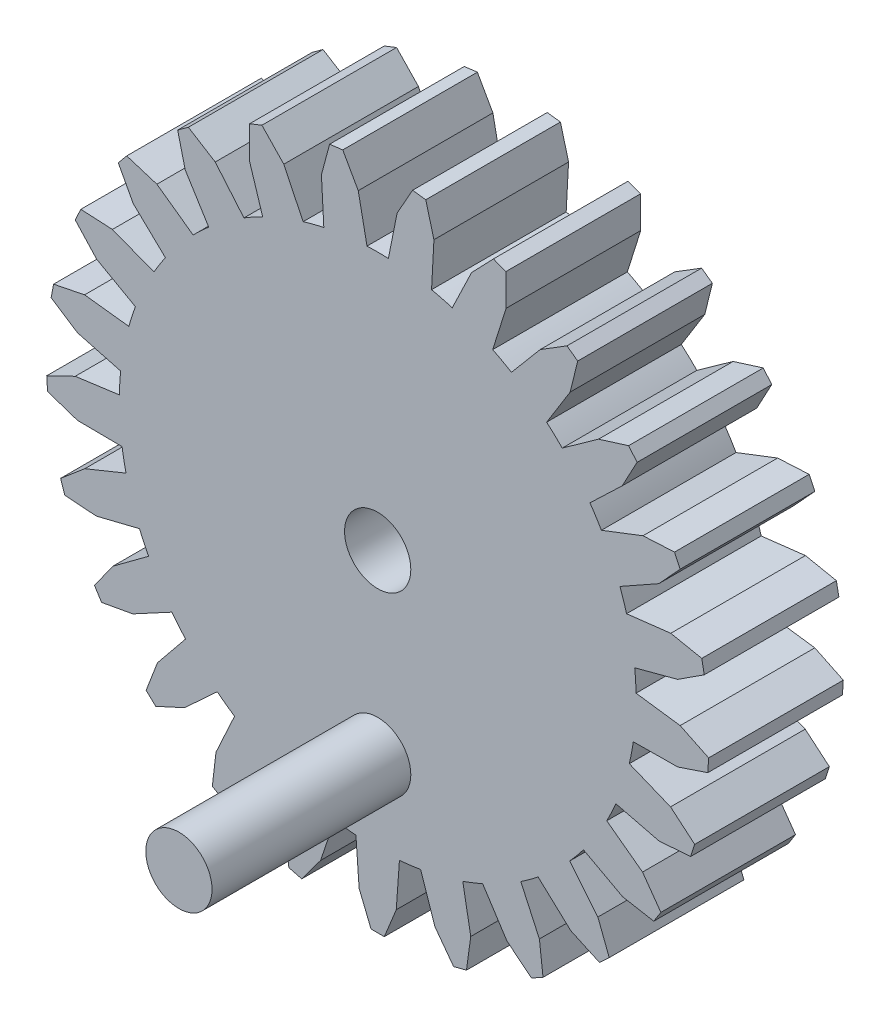
SolidWorks part; units mm, degrees
ref_plane "Front Plane" through (0, 0, 0) normal (0, 0, 1) x (1, 0, 0)
ref_plane "Top Plane" through (0, 0, 0) normal (0, 1, 0) x (1, 0, 0)
ref_plane "Right Plane" through (0, 0, 0) normal (1, 0, 0) x (0, 0, -1)
sketch "Sketch1" plane through (0, 0, 0) normal (0, 0, 1) x (1, 0, 0)
  line L0 (19.9866, -11.0253) -> (17.2857, -9.0253)
  line L1 (0, -24.9917) -> (0.5, -24.9917)
  line L2 (0, -24.9917) -> (-0.5, -24.9917)
  line L3 (0.5, -24.9917) -> (1.4004, -22.7829)
  line L4 (1.4004, -22.7829) -> (1.6418, -19.4308)
  line L5 (21.3691, -12.9691) -> (19.9866, -11.0253)
  line L6 (-4.3095, -22.4154) -> (-3.242, -19.2286)
  line L7 (-5.7309, -24.3309) -> (-4.3095, -22.4154)
  line L8 (20.8333, -13.8134) -> (18.4859, -13.3901)
  line L9 (18.4859, -13.3901) -> (15.5262, -11.7977)
  line L10 (-6.6995, -24.0822) -> (-7.0222, -21.7189)
  line L11 (-7.0222, -21.7189) -> (-6.4225, -18.412)
  line L12 (21.1012, -13.3912) -> (20.8333, -13.8134)
  line L13 (21.1012, -13.3912) -> (21.3691, -12.9691)
  line L14 (-6.2152, -24.2066) -> (-6.6995, -24.0822)
  line L15 (-6.2152, -24.2066) -> (-5.7309, -24.3309)
  line L16 (16.6168, -15.6494) -> (14.4981, -13.0405)
  line L17 (17.4725, -17.8759) -> (16.6168, -15.6494)
  line L18 (-9.7486, -20.6394) -> (-7.9221, -17.8182)
  line L19 (-11.6017, -22.1413) -> (-9.7486, -20.6394)
  line L20 (16.7435, -18.5604) -> (14.5751, -17.5666)
  line L21 (14.5751, -17.5666) -> (12.1045, -15.2883)
  line L22 (-12.478, -21.6595) -> (-12.2029, -19.2902)
  line L23 (-12.2029, -19.2902) -> (-10.7996, -16.2364)
  line L24 (17.108, -18.2182) -> (16.7435, -18.5604)
  line L25 (17.108, -18.2182) -> (17.4725, -17.8759)
  line L26 (-12.0398, -21.9004) -> (-12.478, -21.6595)
  line L27 (-12.0398, -21.9004) -> (-11.6017, -22.1413)
  line L28 (12.2029, -19.2902) -> (10.7996, -16.2364)
  line L29 (12.478, -21.6595) -> (12.2029, -19.2902)
  line L30 (-14.5751, -17.5666) -> (-12.1045, -15.2883)
  line L31 (-16.7435, -18.5604) -> (-14.5751, -17.5666)
  line L32 (11.6017, -22.1413) -> (9.7486, -20.6394)
  line L33 (9.7486, -20.6394) -> (7.9221, -17.8182)
  line L34 (-17.4725, -17.8759) -> (-16.6168, -15.6494)
  line L35 (-16.6168, -15.6494) -> (-14.4981, -13.0405)
  line L36 (12.0398, -21.9004) -> (11.6017, -22.1413)
  line L37 (12.0398, -21.9004) -> (12.478, -21.6595)
  line L38 (-17.108, -18.2182) -> (-17.4725, -17.8759)
  line L39 (-17.108, -18.2182) -> (-16.7435, -18.5604)
  line L40 (7.0222, -21.7189) -> (6.4225, -18.412)
  line L41 (6.6995, -24.0822) -> (7.0222, -21.7189)
  line L42 (-18.4859, -13.3901) -> (-15.5262, -11.7977)
  line L43 (-20.8333, -13.8134) -> (-18.4859, -13.3901)
  line L44 (5.7309, -24.3309) -> (4.3095, -22.4154)
  line L45 (4.3095, -22.4154) -> (3.242, -19.2286)
  line L46 (-21.3691, -12.9691) -> (-19.9866, -11.0253)
  line L47 (-19.9866, -11.0253) -> (-17.2857, -9.0253)
  line L48 (6.2152, -24.2066) -> (5.7309, -24.3309)
  line L49 (6.2152, -24.2066) -> (6.6995, -24.0822)
  line L50 (-21.1012, -13.3912) -> (-21.3691, -12.9691)
  line L51 (-21.1012, -13.3912) -> (-20.8333, -13.8134)
  line L54 (-21.2351, -8.3721) -> (-17.9724, -7.5659)
  line L55 (-23.614, -8.1984) -> (-21.2351, -8.3721)
  line L58 (-23.923, -7.2473) -> (-22.1005, -5.7085)
  line L59 (-22.1005, -5.7085) -> (-18.9871, -4.443)
  line L62 (-23.7685, -7.7229) -> (-23.923, -7.2473)
  line L63 (-23.7685, -7.7229) -> (-23.614, -8.1984)
  line L66 (-22.65, -2.8282) -> (-19.2893, -2.8586)
  line L67 (-24.911, -2.0683) -> (-22.65, -2.8282)
  line L70 (-24.9738, -1.0702) -> (-22.8259, -0.0329)
  line L71 (-22.8259, -0.0329) -> (-19.4955, 0.4185)
  line L74 (-24.9424, -1.5692) -> (-24.9738, -1.0702)
  line L75 (-24.9424, -1.5692) -> (-24.911, -2.0683)
  line L78 (-22.6417, 2.8935) -> (-19.3942, 2.0282)
  line L79 (-24.6427, 4.1918) -> (-22.6417, 2.8935)
  line L82 (-24.4554, 5.1741) -> (-22.1169, 5.6447)
  line L83 (-22.1169, 5.6447) -> (-18.7789, 5.2537)
  line L85 (-0.5, -24.9917) -> (-1.4004, -22.7829)
  line L86 (-1.4004, -22.7829) -> (-1.6418, -19.4308)
  line L87 (-24.549, 4.683) -> (-24.4554, 5.1741)
  line L88 (-24.549, 4.683) -> (-24.6427, 4.1918)
  line L89 (-21.2108, 8.4334) -> (-18.2805, 6.7877)
  line L90 (-22.8261, 10.1885) -> (-21.2108, 8.4334)
  line L91 (-22.4003, 11.0934) -> (-20.0183, 10.9676)
  line L92 (-20.0183, 10.9676) -> (-16.8824, 9.7588)
  line L93 (-22.6132, 10.641) -> (-22.4003, 11.0934)
  line L94 (-22.6132, 10.641) -> (-22.8261, 10.1885)
  line L95 (-18.4471, 13.4433) -> (-16.0182, 11.1206)
  line L96 (-19.5752, 15.5451) -> (-18.4471, 13.4433)
  line L97 (-18.9377, 16.3156) -> (-16.6619, 15.6014)
  line L98 (-16.6619, 15.6014) -> (-13.9251, 13.6507)
  line L99 (-19.2564, 15.9303) -> (-18.9377, 16.3156)
  line L100 (-19.2564, 15.9303) -> (-19.5752, 15.5451)
  line L101 (-14.5244, 17.6086) -> (-12.7494, 14.7548)
  line L102 (-15.0943, 19.9248) -> (-14.5244, 17.6086)
  line L103 (-14.2853, 20.5126) -> (-12.2585, 19.2549)
  line L104 (-12.2585, 19.2549) -> (-10.0929, 16.6848)
  line L105 (-14.6898, 20.2187) -> (-14.2853, 20.5126)
  line L106 (-14.6898, 20.2187) -> (-15.0943, 19.9248)
  line L107 (-9.689, 20.6675) -> (-8.6794, 17.4619)
  line L108 (-9.665, 23.0526) -> (-9.689, 20.6675)
  line L109 (-8.7352, 23.4208) -> (-7.0849, 21.6985)
  line L110 (-7.0849, 21.6985) -> (-5.6264, 18.6707)
  line L111 (-9.2001, 23.2367) -> (-8.7352, 23.4208)
  line L112 (-9.2001, 23.2367) -> (-9.665, 23.0526)
  line L113 (-4.2448, 22.4277) -> (-4.0642, 19.0718)
  line L114 (-3.6283, 24.732) -> (-4.2448, 22.4277)
  line L115 (-2.6362, 24.8573) -> (-1.4661, 22.7787)
  line L116 (-1.4661, 22.7787) -> (-0.8065, 19.4833)
  line L117 (-3.1323, 24.7946) -> (-2.6362, 24.8573)
  line L118 (-3.1323, 24.7946) -> (-3.6283, 24.732)
  line L119 (1.4661, 22.7787) -> (0.8065, 19.4833)
  line L120 (2.6362, 24.8573) -> (1.4661, 22.7787)
  line L121 (3.6283, 24.732) -> (4.2448, 22.4277)
  line L122 (4.2448, 22.4277) -> (4.0642, 19.0718)
  line L123 (3.1323, 24.7946) -> (3.6283, 24.732)
  line L124 (3.1323, 24.7946) -> (2.6362, 24.8573)
  line L125 (7.0849, 21.6985) -> (5.6264, 18.6707)
  line L126 (8.7352, 23.4208) -> (7.0849, 21.6985)
  line L127 (9.665, 23.0526) -> (9.689, 20.6675)
  line L128 (9.689, 20.6675) -> (8.6794, 17.4619)
  line L129 (9.2001, 23.2367) -> (9.665, 23.0526)
  line L130 (9.2001, 23.2367) -> (8.7352, 23.4208)
  line L131 (12.2585, 19.2549) -> (10.0929, 16.6848)
  line L132 (14.2853, 20.5126) -> (12.2585, 19.2549)
  line L133 (15.0943, 19.9248) -> (14.5244, 17.6086)
  line L134 (14.5244, 17.6086) -> (12.7494, 14.7548)
  line L135 (14.6898, 20.2187) -> (15.0943, 19.9248)
  line L136 (14.6898, 20.2187) -> (14.2853, 20.5126)
  line L137 (16.6619, 15.6014) -> (13.9251, 13.6507)
  line L138 (18.9377, 16.3156) -> (16.6619, 15.6014)
  line L139 (19.5752, 15.5451) -> (18.4471, 13.4433)
  line L140 (18.4471, 13.4433) -> (16.0182, 11.1206)
  line L141 (19.2564, 15.9303) -> (19.5752, 15.5451)
  line L142 (19.2564, 15.9303) -> (18.9377, 16.3156)
  line L143 (20.0183, 10.9676) -> (16.8824, 9.7588)
  line L144 (22.4003, 11.0934) -> (20.0183, 10.9676)
  line L145 (22.8261, 10.1885) -> (21.2108, 8.4334)
  line L146 (21.2108, 8.4334) -> (18.2805, 6.7877)
  line L147 (22.6132, 10.641) -> (22.8261, 10.1885)
  line L148 (22.6132, 10.641) -> (22.4003, 11.0934)
  line L149 (22.1169, 5.6447) -> (18.7789, 5.2537)
  line L150 (24.4554, 5.1741) -> (22.1169, 5.6447)
  line L151 (24.6427, 4.1918) -> (22.6417, 2.8935)
  line L152 (22.6417, 2.8935) -> (19.3942, 2.0282)
  line L153 (24.549, 4.683) -> (24.6427, 4.1918)
  line L154 (24.549, 4.683) -> (24.4554, 5.1741)
  line L155 (22.8259, -0.0329) -> (19.4955, 0.4185)
  line L156 (24.9738, -1.0702) -> (22.8259, -0.0329)
  line L157 (24.911, -2.0683) -> (22.65, -2.8282)
  line L158 (22.65, -2.8282) -> (19.2893, -2.8586)
  line L159 (24.9424, -1.5692) -> (24.911, -2.0683)
  line L160 (24.9424, -1.5692) -> (24.9738, -1.0702)
  line L161 (22.1005, -5.7085) -> (18.9871, -4.443)
  line L162 (23.923, -7.2473) -> (22.1005, -5.7085)
  line L163 (23.614, -8.1984) -> (21.2351, -8.3721)
  line L164 (21.2351, -8.3721) -> (17.9724, -7.5659)
  line L165 (23.7685, -7.7229) -> (23.614, -8.1984)
  line L166 (23.7685, -7.7229) -> (23.923, -7.2473)
  circle A0 centre (0, 0) radius 19.5
  circle A2 centre (0, 0) radius 19.5
  point P106 (0, 0)
  point P117 (0, 0)
  point P235 (0, 0)
  dimension "D1" = 39
  dimension "D2" = 0.5
  dimension "D3" = 0.5
  dimension "D4" = 25
extrude "Boss-Extrude1" add sketch "Sketch1" along normal blind 10.16
sketch "Sketch2" plane through (0, 0, 10.16) normal (0, 0, 1) x (1, 0, 0)
  circle A0 centre (0, 0) radius 2.5
  dimension "D1" = 5
extrude "Cut-Extrude1" cut sketch "Sketch2" against normal blind 10.16
sketch "Sketch4" plane through (0, 0, 10.16) normal (0, 0, 1) x (1, 0, 0)
  circle A0 centre (0, 0) radius 25.05 construction
  dimension "D1" = 50.1
sketch "Sketch5" plane through (0, 0, 10.16) normal (0, 0, 1) x (1, 0, 0)
  circle A0 centre (0, -13.4062) radius 2.5
  dimension "D1" = 5
extrude "Boss-Extrude2" add sketch "Sketch5" along normal blind 15
